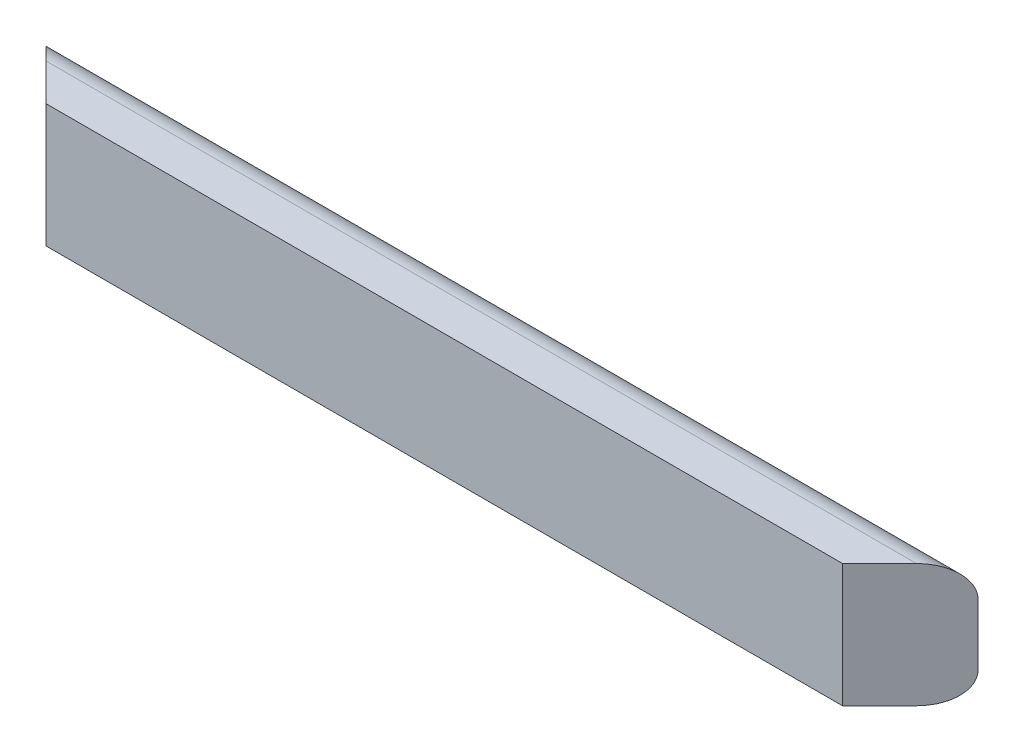
SolidWorks part; units mm, degrees
material "Custom Plastic"
ref_plane "Front Plane" through (0, 0, 0) normal (0, 0, 1) x (1, 0, 0)
ref_plane "Top Plane" through (0, 0, 0) normal (0, 1, 0) x (1, 0, 0)
ref_plane "Right Plane" through (0, 0, 0) normal (1, 0, 0) x (0, 0, -1)
sketch "Sketch1" plane through (0, 0, 0) normal (1, 0, 0) x (0, 0, -1)
  line L0 (6.35, 127) -> (38.1, 127)
  line L1 (0, 0) -> (6.35, 0)
  line L2 (0, 0) -> (0, 127)
  line L3 (0, 127) -> (6.35, 127)
  line L5 (69.85, 95.25) -> (69.85, 31.75)
  line L6 (38.1, 0) -> (6.35, 0)
  arc A0 (69.85, 95.25) -> (38.1, 127) centre (38.1, 95.25) ccw
  arc A1 (38.1, 0) -> (69.85, 31.75) centre (38.1, 31.75) ccw
  dimension "D3" = 63.5
  dimension "D5" = 31.75
  dimension "D1" = 127
  dimension "D2" = 6.35
  dimension "D4" = 31.75
extrude "Boss-Extrude1" add sketch "Sketch1" along normal blind 480.1871 and the other way blind 480.1871
sketch "Sketch2" plane through (0, 127, 0) normal (0, 1, 0) x (1, 0, 0)
  line L0 (480.1871, 69.85) -> (410.3371, 0)
  line L1 (-55, 0) -> (55, 0) construction
  line L2 (-480.1871, 69.85) -> (-410.3371, 0)
  line L3 (-480.1871, 69.85) -> (-480.1871, 0)
  line L4 (-480.1871, 38.1) -> (-480.1871, 0) construction
  line L5 (-480.1871, 0) -> (-410.3371, 0)
  line L6 (480.1871, 69.85) -> (480.1871, 0)
  line L7 (480.1871, 38.1) -> (480.1871, 0) construction
  line L8 (480.1871, 0) -> (410.3371, 0)
  dimension "D1" = 45
  dimension "D2" = 45
extrude "Cut-Extrude1" cut sketch "Sketch2" against normal through all
sketch "Sketch4" plane through (0, 0, -69.85) normal (0, 0, -1) x (-1, 0, 0)
  line L0 (0, 38.4175) -> (0, -38.4175) construction
  line L1 (38.4175, 0) -> (-38.4175, 0) construction
  text T0 "3597" font "Arial" height in points 250
  dimension "D1" = 144.78
  dimension "D2" = 31.75
extrude "Boss-Extrude3" add sketch "Sketch4" along normal blind 0.254
